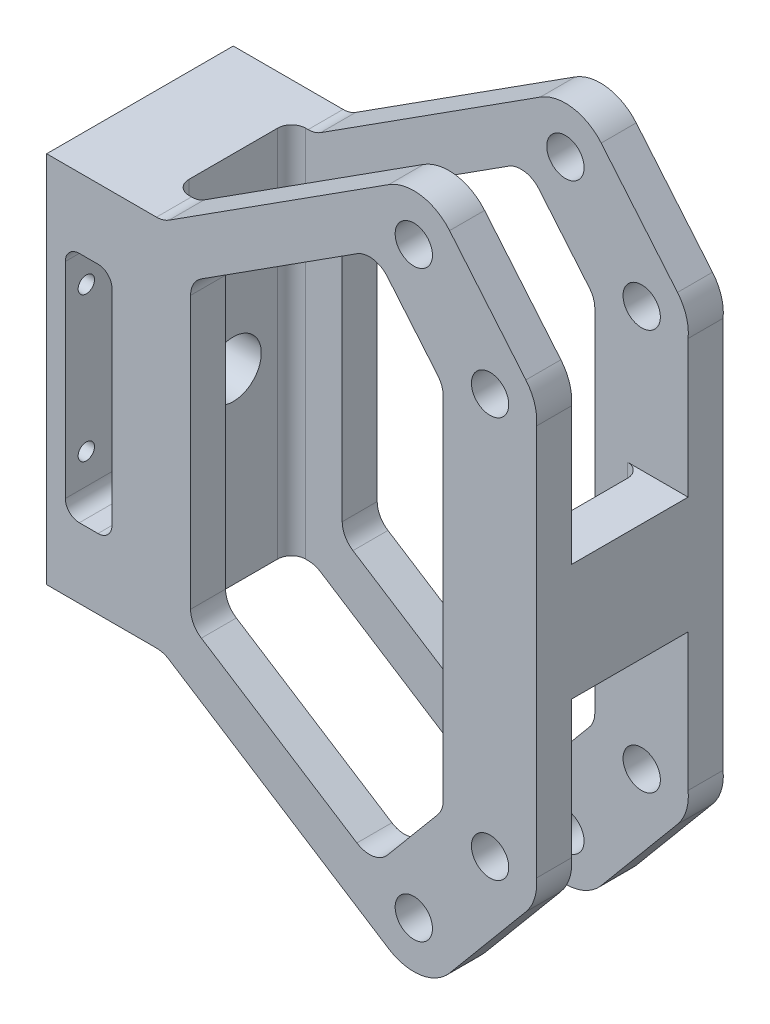
SolidWorks part; units mm, degrees
ref_plane "Front Plane" through (0, 0, 0) normal (0, 0, 1) x (1, 0, 0)
ref_plane "Top Plane" through (0, 0, 0) normal (0, 1, 0) x (1, 0, 0)
ref_plane "Right Plane" through (0, 0, 0) normal (1, 0, 0) x (0, 0, -1)
sketch "Sketch1" plane through (0, 0, 0) normal (0, 0, 1) x (1, 0, 0)
  line L0 (25, 0) -> (73.3089, -30.9223)
  line L1 (0, 0) -> (25, 0)
  line L2 (0, 0) -> (0, 80)
  line L3 (0, 80) -> (25, 80)
  line L4 (105, 0) -> (105, 80)
  line L5 (86.3709, -28.9153) -> (102.7209, -9.3653)
  line L6 (0, 40) -> (105, 40) construction
  line L7 (105, 0) -> (105, -1.9513)
  line L8 (105, 80) -> (105, 81.9513)
  line L9 (86.3709, 108.9153) -> (102.7209, 89.3653)
  line L10 (25, 80) -> (73.3089, 110.9223)
  line L11 (30.8528, 71.8732) -> (30.8528, 8.1268)
  line L12 (70.2091, 97.065) -> (85, 79.3793)
  line L13 (70.2091, -17.065) -> (85, 0.6207)
  line L14 (85, 0.6207) -> (85, 79.3793)
  line L15 (30.8528, 8.1268) -> (70.2091, -17.065)
  line L18 (30.8528, 71.8732) -> (70.2091, 97.065)
  line L28 (30.3911, 71.5777) -> (78.7, 102.5) construction
  circle A0 centre (78.7, -22.5) radius 4
  circle A1 centre (95.05, -2.95) radius 4
  arc A2 (73.3089, -30.9223) -> (86.3709, -28.9153) centre (78.7, -22.5) ccw
  arc A3 (102.7209, -9.3653) -> (105, -1.9513) centre (95.05, -2.95) ccw
  circle A4 centre (78.7, 102.5) radius 4
  circle A5 centre (95.05, 82.95) radius 4
  arc A6 (102.7209, 89.3653) -> (105, 81.9513) centre (95.05, 82.95) cw
  arc A7 (73.3089, 110.9223) -> (86.3709, 108.9153) centre (78.7, 102.5) cw
  point P28 (85, 40)
  point P32 (30.8528, 40)
  dimension "D5" = 8
  dimension "D8" = 8
  dimension "D9" = 20
  dimension "D10" = 20
  dimension "D1" = 80
  dimension "D2" = 105
  dimension "D3" = 22.5
  dimension "D4" = 78.7
  dimension "D6" = 2.95
  dimension "D7" = 95.05
  dimension "D11" = 25
  dimension "D12" = 80
  dimension "D16" = 20
  dimension "D13" = 20
  dimension "D15" = 30.8528
  dimension "D14" = 10
extrude "Boss-Extrude1" add sketch "Sketch1" against normal blind 40
sketch "Sketch2" plane through (0, 0, 0) normal (0, 1, 0) x (1, 0, 0)
  line L0 (0, 40) -> (0, 0) construction
  line L1 (20, 32.5) -> (120, 32.5)
  line L2 (20, 32.5) -> (20, 7.5)
  line L3 (20, 7.5) -> (120, 7.5)
  line L4 (120, 32.5) -> (120, 7.5)
  line L5 (102.7209, 0) -> (86.3709, 0) construction
  dimension "D1" = 20
  dimension "D2" = 25
  dimension "D3" = 7.5
  dimension "D4" = 100
extrude "Cut-Extrude1" cut sketch "Sketch2" against normal through all both and the other way through all
sketch "Sketch3" plane through (105, 0, 0) normal (1, 0, 0) x (0, 0, -1)
  line L0 (0, -1.9513) -> (0, 81.9513) construction
  line L1 (0, 40) -> (40, 40) construction
  line L2 (40, -1.9513) -> (40, 81.9513) construction
  line L4 (7.5, 27.5) -> (32.5, 27.5)
  line L5 (7.5, 27.5) -> (7.5, 52.5)
  line L6 (7.5, 52.5) -> (32.5, 52.5)
  line L7 (32.5, 27.5) -> (32.5, 52.5)
  line L8 (7.5, 27.5) -> (32.5, 52.5) construction
  line L9 (7.5, 52.5) -> (32.5, 27.5) construction
  point P6 (20, 40)
  dimension "D1" = 25
  dimension "D2" = 25
extrude "Boss-Extrude2" add sketch "Sketch3" against normal blind 10
sketch "Sketch4" plane through (0, 0, 0) normal (-1, 0, 0) x (0, 0, 1)
  line L2 (0, 80) -> (0, 0) construction
  line L3 (-40, 80) -> (0, 80) construction
  circle A0 centre (-20, 40) radius 6
  dimension "D1" = 12
  dimension "D2" = 20
  dimension "D3" = 40
extrude "Cut-Extrude2" cut sketch "Sketch4" against normal blind 100
fillet "Fillet1" radius 5 16 edges at (25, 0, -3.75) (25, 0, -36.25) (25, 80, -36.25) (25, 80, -3.75) (30.8528, 71.8732, -3.75) (30.8528, 8.1268, -36.25) (30.8528, 71.8732, -36.25) (70.2091, 97.065, -36.25) (85, 79.3793, -36.25) (70.2091, 97.065, -3.75) (85, 79.3793, -3.75) (70.2091, -17.065, -36.25) (85, 0.6207, -36.25) (85, 0.6207, -3.75) (70.2091, -17.065, -3.75) (30.8528, 8.1268, -3.75)
fillet "Fillet2" radius 3 4 edges at (20, 40, -32.5) (20, 40, -7.5) (95, 40, -32.5) (95, 40, -7.5)
sketch "Sketch5" plane through (0, 0, 0) normal (-1, 0, 0) x (0, 0, 1)
  line L1 (-35.5, 24.5) -> (-4.5, 24.5) construction
  line L2 (-35.5, 24.5) -> (-35.5, 55.5) construction
  line L3 (-35.5, 55.5) -> (-4.5, 55.5) construction
  line L4 (-4.5, 24.5) -> (-4.5, 55.5) construction
  line L5 (-35.5, 24.5) -> (-4.5, 55.5) construction
  line L6 (-35.5, 55.5) -> (-4.5, 24.5) construction
  circle A0 centre (-35.5, 55.5) radius 1.75
  circle A1 centre (-4.5, 55.5) radius 1.75
  circle A2 centre (-35.5, 24.5) radius 1.75
  circle A3 centre (-4.5, 24.5) radius 1.75
  point P0 (-20, 40)
  dimension "D3" = 3.5
  dimension "D4" = 3.5
  dimension "D5" = 3.5
  dimension "D6" = 3.5
  dimension "D1" = 31
  dimension "D2" = 31
extrude "Cut-Extrude3" cut sketch "Sketch5" against normal blind 10
sketch "Sketch7" plane through (0, 0, 0) normal (0, 0, 1) x (1, 0, 0)
  line L0 (0, 40) -> (30.8528, 40) construction
  line L1 (0, 80) -> (0, 0) construction
  line L3 (4, 65) -> (4, 15)
  line L4 (4, 15) -> (14, 15)
  line L5 (14, 15) -> (14, 65)
  line L6 (14, 65) -> (4, 65)
  dimension "D1" = 25
  dimension "D2" = 25
  dimension "D3" = 4
  dimension "D4" = 10
extrude "Cut-Extrude4" cut sketch "Sketch7" against normal blind 10
fillet "Fillet3" radius 3 4 edges at (14, 15, -5) (4, 15, -5) (14, 65, -5) (4, 65, -5)
ref_plane "Plane1" through (0, 0, -20) normal (0, 0, 1) x (1, 0, 0)
mirror "Mirror1" about plane through (0, 0, -20) normal (0, 0, 1) of "Fillet3", "Cut-Extrude4"
sketch "Sketch8" plane through (0, 0, 0) normal (-1, 0, 0) x (0, 0, 1)
  circle A0 centre (-20, 40) radius 12.5
  dimension "D1" = 25
extrude "Cut-Extrude5" cut sketch "Sketch8" against normal blind 3
